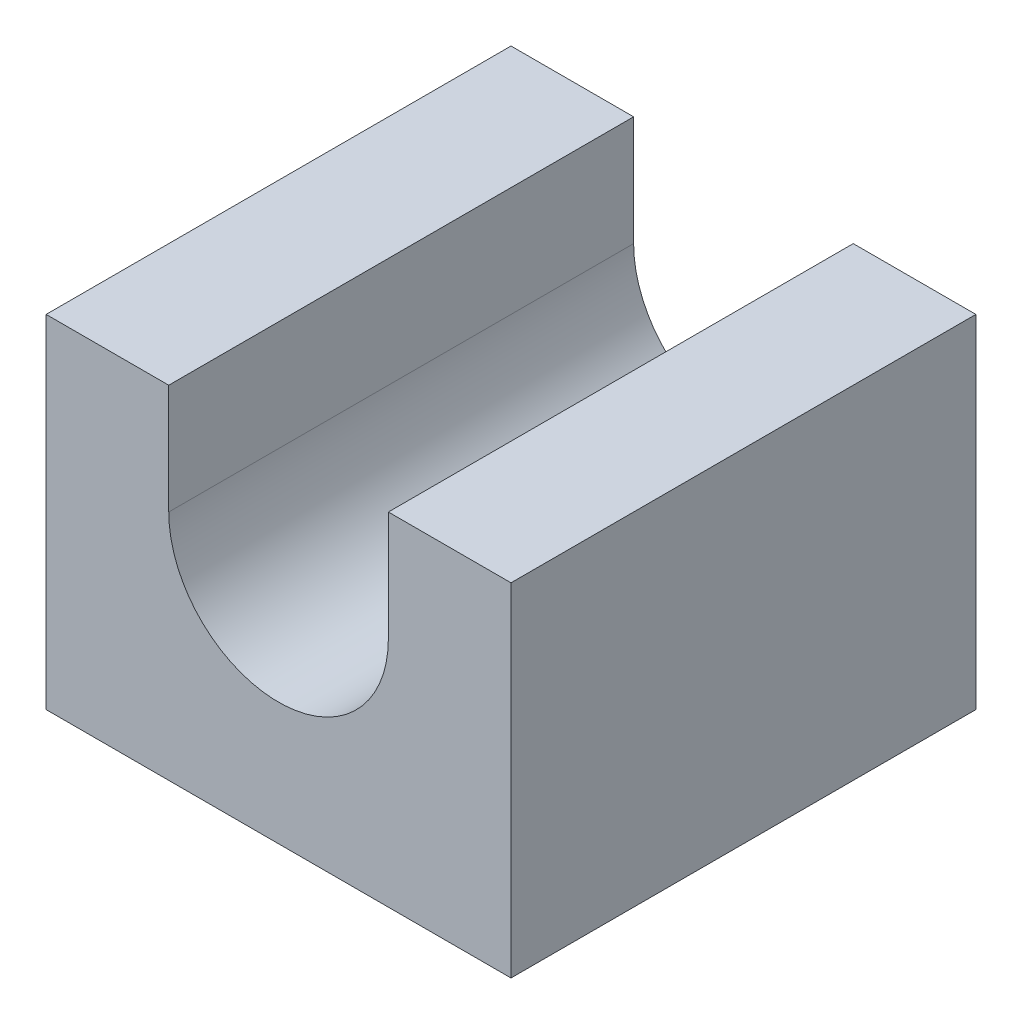
SolidWorks part; units mm, degrees
ref_plane "Front Plane" through (0, 0, 0) normal (0, 0, 1) x (1, 0, 0)
ref_plane "Top Plane" through (0, 0, 0) normal (0, 1, 0) x (1, 0, 0)
ref_plane "Right Plane" through (0, 0, 0) normal (1, 0, 0) x (0, 0, -1)
sketch "Sketch2" plane through (0, 0, 0) normal (0, 0, 1) x (1, 0, 0)
  line L0 (8.375, 23.375) -> (0, 23.375)
  line L1 (0, 0) -> (31.75, 0)
  line L2 (0, 0) -> (0, 31.75)
  line L3 (0, 31.75) -> (31.75, 31.75)
  line L4 (31.75, 0) -> (31.75, 31.75)
  line L5 (23.375, 23.375) -> (31.75, 23.375)
  line L7 (8.375, 15.875) -> (8.375, 23.375)
  line L8 (23.375, 15.875) -> (23.375, 23.375)
  circle A0 centre (15.875, 15.875) radius 7.5
  dimension "D1" = 31.75
  dimension "D2" = 31.75
extrude "Boss-Extrude2" add sketch "Sketch2" along normal blind 31.75 contours A0 L7 L0 L2 L1 L4 L5 L8
